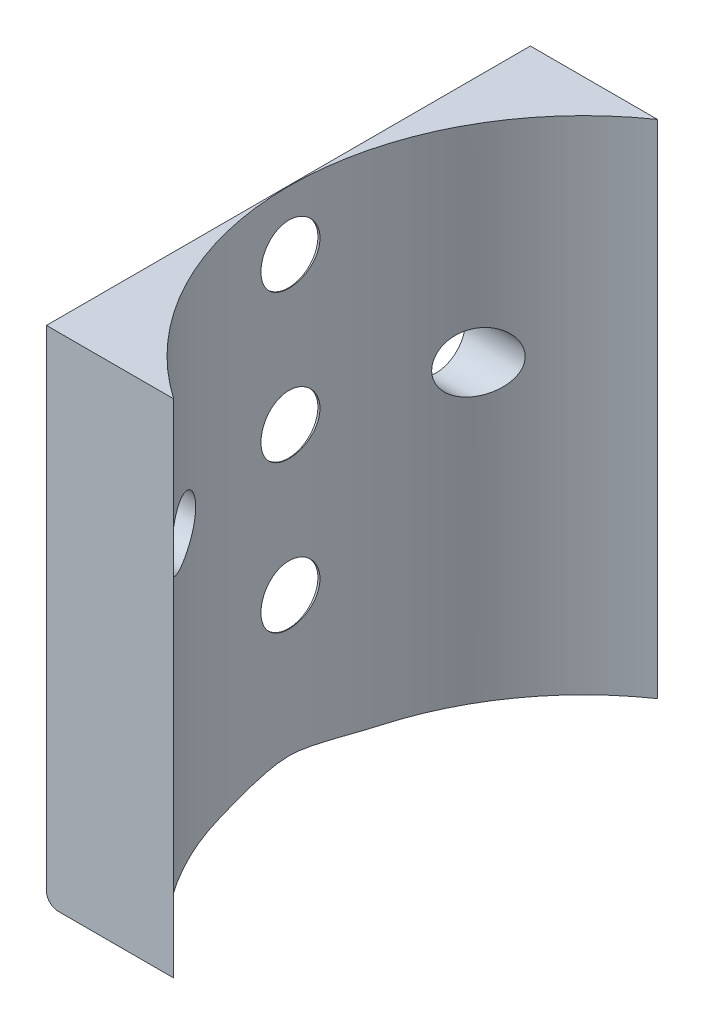
SolidWorks part; units mm, degrees
material "Бутил"
ref_plane "Спереди" through (0, 0, 0) normal (0, 0, 1) x (1, 0, 0)
ref_plane "Сверху" through (0, 0, 0) normal (0, 1, 0) x (1, 0, 0)
ref_plane "Справа" through (0, 0, 0) normal (1, 0, 0) x (0, 0, -1)
other "Configuration Table"
sketch "Эскиз1" plane through (0, 0, 0) normal (0, 1, 0) x (1, 0, 0)
  line L1 (12.5, -20.5) -> (-12.5, -20.5)
  line L2 (12.5, -20.5) -> (12.5, 20.5)
  line L3 (12.5, 20.5) -> (-12.5, 20.5)
  line L4 (-12.5, -20.5) -> (-12.5, 20.5)
  line L5 (12.5, -20.5) -> (-12.5, 20.5) construction
  line L6 (12.5, 20.5) -> (-12.5, -20.5) construction
  point P0 (0, 0)
  dimension "D1" = 25
  dimension "D2" = 41
extrude "Бобышка-Вытянуть1" add sketch "Эскиз1" along normal blind 42.5
fillet "Скругление1" radius 1 1 edges at (-12.5, 0, 0)
sketch "Эскиз2" plane through (0, 42.5, 0) normal (0, 1, 0) x (1, 0, 0)
  line L0 (12.5, -20.5) -> (12.5, 20.5) construction
  circle A0 centre (12.5, 0) radius 24.95
  dimension "D1" = 49.9
extrude "Вырез-Вытянуть1" cut sketch "Эскиз2" against normal blind 42.5
sketch "Эскиз3" plane through (-12.5, 0, 0) normal (-1, 0, 0) x (0, 0, 1)
  line L0 (-20.5, 42.5) -> (20.5, 42.5) construction
  line L1 (20.5, 42.5) -> (20.5, 1) construction
  line L2 (0, 25) -> (-12.5, 25) construction
  circle A0 centre (0, 25) radius 12.5 construction
  circle A1 centre (-12.5, 25) radius 2.5
  circle A3 centre (0, 37.5) radius 2.5
  circle A5 centre (12.5, 25) radius 2.5
  circle A6 centre (0, 25) radius 12.5 construction
  circle A7 centre (0, 12.5) radius 2.5
  circle A8 centre (0, 25) radius 12.5 [skipped]
  circle A9 centre (0, 25) radius 12.5 [skipped]
  circle A10 centre (0, 25) radius 2.5
  dimension "D1" = 25
  dimension "D4" = 5
  dimension "D6" = 5
  dimension "D2" = 17.5
  dimension "D3" = 20.5
  dimension "D5" = 4
extrude "Вырез-Вытянуть2" cut sketch "Эскиз3" against normal blind 10 contours A10 | A3 | A1 | A5 | A7
